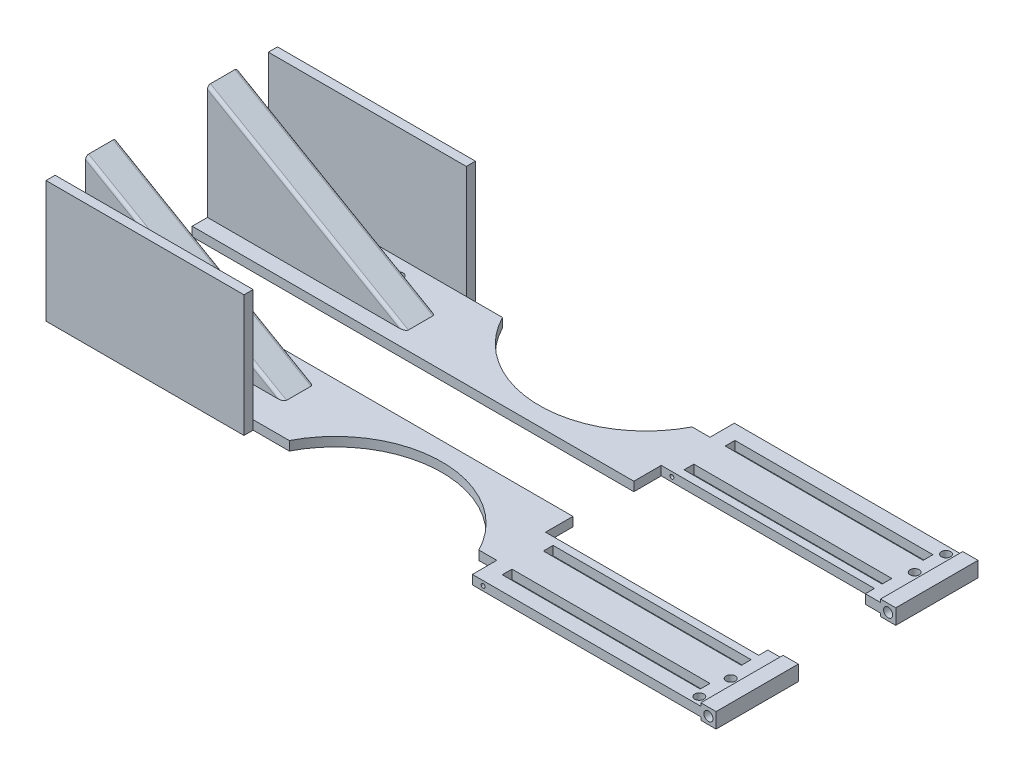
SolidWorks part; units mm, degrees
ref_plane "前视基准面" through (0, 0, 0) normal (0, 0, 1) x (1, 0, 0)
ref_plane "上视基准面" through (0, 0, 0) normal (0, 1, 0) x (1, 0, 0)
ref_plane "右视基准面" through (0, 0, 0) normal (1, 0, 0) x (0, 0, -1)
sketch "草图1" plane through (0, 0, 0) normal (0, 1, 0) x (1, 0, 0)
  line L0 (-92.9537, 0) -> (133.3808, 0) construction
  line L1 (0, 79.573) -> (0, -79.8577) construction
  line L2 (-82.7046, -35) -> (-82.7046, 35)
  line L3 (-82.7046, 35) -> (137.2954, 35)
  line L4 (137.2954, 35) -> (137.2954, -35)
  line L5 (-82.7046, -35) -> (137.2954, -35)
  point P10 (137.2954, 0)
  point P11 (-82.7046, 0)
  dimension "D1" = 70
  dimension "D2" = 220
extrude "凸台-拉伸1" add sketch "草图1" along normal blind 3
sketch "草图2" plane through (0, 0, 0) normal (0, 0, 1) x (1, 0, 0)
  line L0 (-2.7046, 3) -> (-2.7046, 43.2178) construction
  line L2 (59.2954, 3) -> (59.2954, 47.8617) construction
  line L3 (-82.7046, 3) -> (-82.7046, 0) construction
  line L5 (-82.7046, 40.5278) -> (-82.7046, 3)
  line L10 (-82.7046, 3) -> (-17.7046, 3)
  line L11 (-82.7046, 40.5278) -> (-17.7046, 3)
  dimension "D1" = 62
  dimension "D2" = 80
  dimension "D3" = 30
  dimension "D4" = 65
extrude "凸台-拉伸2" add sketch "草图2" along normal blind 25 and the other way blind 25
sketch "草图6" plane through (-82.7046, 0, 0) normal (-1, 0, 0) x (0, 0, 1)
  line L0 (0, 40.5278) -> (0, 0) construction
  line L1 (-25, 40.5278) -> (25, 40.5278) construction
  line L2 (-15, 40.5278) -> (-15, 3)
  line L3 (-15, 3) -> (15, 3)
  line L4 (15, 3) -> (15, 40.5278)
  line L5 (15, 40.5278) -> (-15, 40.5278)
  dimension "D1" = 15
  dimension "D2" = 15
extrude "切除-拉伸4" cut sketch "草图6" against normal through all
sketch "草图7" plane through (0, 3, 0) normal (0, 1, 0) x (1, 0, 0)
  line L0 (-2.7046, 35) -> (-2.7046, -35) construction
  line L4 (137.2954, 35) -> (-82.7046, 35) construction
  line L5 (-82.7046, -35) -> (137.2954, -35) construction
  line L6 (-82.7046, 35) -> (-82.7046, 25) construction
  line L7 (53.2954, 35) -> (53.2954, -35) construction
  line L8 (25.2954, 88.1076) -> (25.2954, -100.7895) construction
  line L9 (-82.7046, 0) -> (117.2954, 0) construction
  line L11 (-82.7046, 15) -> (-82.7046, -15) construction
  circle A0 centre (25.2954, 51) radius 35
  circle A1 centre (25.2954, -51) radius 35
  dimension "D4" = 70
  dimension "D1" = 80
  dimension "D2" = 56
  dimension "D3" = 28
  dimension "D5" = 102
extrude "切除-拉伸5" cut sketch "草图7" against normal through all
sketch "草图8" plane through (-82.7046, 0, 0) normal (-1, 0, 0) x (0, 0, 1)
  line L0 (35, 0) -> (35, 40)
  line L1 (35, 40) -> (38, 40)
  line L2 (38, 40) -> (38, 0)
  line L3 (38, 0) -> (35, 0)
  line L4 (0, 36.5043) -> (0, -13.2047) construction
  line L5 (-38, 0) -> (-35, 0)
  line L6 (-38, 40) -> (-38, 0)
  line L7 (-35, 40) -> (-38, 40)
  line L8 (-35, 0) -> (-35, 40)
  dimension "D1" = 3
  dimension "D2" = 40
extrude "凸台-拉伸3" add sketch "草图8" against normal blind 65
sketch "草图9" plane through (0, 3, 0) normal (0, 1, 0) x (1, 0, 0)
  line L0 (-82.7046, 15) -> (-82.7046, -15) construction
  line L1 (-82.7046, 0) -> (117.2954, 0) construction
  circle A0 centre (-74.7668, 29.8601) radius 1.5
  circle A1 centre (-54.7668, 29.8601) radius 1.5
  circle A2 centre (-34.7668, 29.8601) radius 1.5
  circle A3 centre (-34.7668, -29.8601) radius 1.5
  circle A4 centre (-54.7668, -29.8601) radius 1.5
  circle A5 centre (-74.7668, -29.8601) radius 1.5
  dimension "D1" = 3
  dimension "D2" = 3
extrude "切除-拉伸6" cut sketch "草图9" against normal through all
fillet "圆角5" radius 1 4 edges at (-50.2046, 21.7639, -15) (-50.2046, 21.7639, 15) (-50.2046, 21.7639, 25) (-50.2046, 21.7639, -25)
sketch "草图10" plane through (0, 3, 0) normal (0, 1, 0) x (1, 0, 0)
  line L0 (-82.7046, 0) -> (137.2954, 0) construction
  line L1 (-82.7046, 15) -> (-82.7046, -15) construction
  line L2 (137.2954, 35) -> (137.2954, -35) construction
  line L3 (-82.7046, -10) -> (-82.7046, 10)
  line L4 (-82.7046, 10) -> (-17.7046, 10)
  line L5 (-17.7046, 10) -> (-17.7046, -10)
  line L6 (-82.7046, -10) -> (-17.7046, -10)
  point P11 (-17.7046, 0)
  dimension "D1" = 20
extrude "切除-拉伸7" cut sketch "草图10" against normal through all
sketch "草图11" plane through (0, 3, 0) normal (0, 1, 0) x (1, 0, 0)
  line L0 (137.2954, 0) -> (-17.7046, 0) construction
  line L1 (137.2954, -35) -> (137.2954, 35) construction
  line L2 (-17.7046, -10) -> (-17.7046, 10) construction
  line L3 (62.2954, 43) -> (137.2954, 35) construction
  line L4 (137.2954, 35) -> (62.2954, 35)
  line L5 (137.2954, 35) -> (137.2954, 43)
  line L6 (137.2954, 43) -> (62.2954, 43)
  line L7 (62.2954, 35) -> (62.2954, 43)
  line L8 (62.2954, 35) -> (137.2954, 43) construction
  line L9 (137.2954, -35) -> (137.2954, -43)
  line L10 (67.2954, 38.2) -> (132.2954, 38.2)
  line L11 (67.2954, 38.2) -> (67.2954, 35)
  line L12 (67.2954, 35) -> (132.2954, 35)
  line L13 (132.2954, 38.2) -> (132.2954, 35)
  line L14 (67.2954, 38.2) -> (132.2954, 35) construction
  line L15 (67.2954, 35) -> (132.2954, 38.2) construction
  line L16 (137.2954, -43) -> (62.2954, -43)
  line L17 (62.2954, -35) -> (62.2954, -43)
  line L18 (137.2954, -35) -> (62.2954, -35)
  line L19 (67.2954, -35) -> (132.2954, -35)
  line L20 (132.2954, -38.2) -> (132.2954, -35)
  line L21 (67.2954, -38.2) -> (132.2954, -38.2)
  line L22 (67.2954, -38.2) -> (67.2954, -35)
  point P12 (102.2954, 39)
  line M27 (56.4241, -35) -> (137.2954, -35)
  line M29 (137.2954, 35) -> (56.4241, 35)
  dimension "D1" = 75
  dimension "D2" = 3.2
  dimension "D3" = 8
  dimension "D4" = 65
  dimension "D5" = 5
extrude "网球卡槽" add sketch "草图11" against normal blind 3 contours L10 L13 L5 L6 L7 L4 L11 M29 | L21 L22 L17 L16 L9 L20 M27
sketch "草图12" plane through (0, 3, 0) normal (0, 1, 0) x (1, 0, 0)
  line L0 (-17.7046, 0) -> (137.2954, 0) construction
  line L1 (-17.7046, -10) -> (-17.7046, 10) construction
  line L2 (137.2954, -43) -> (137.2954, 43) construction
  line L3 (67.2954, -21.5) -> (67.2954, -24.7)
  line L4 (132.2954, 21.5) -> (67.2954, 21.5)
  line L5 (132.2954, 21.5) -> (132.2954, 24.7)
  line L6 (132.2954, 24.7) -> (67.2954, 24.7)
  line L7 (67.2954, 21.5) -> (67.2954, 24.7)
  line L8 (132.2954, -24.7) -> (67.2954, -24.7)
  line L9 (132.2954, -21.5) -> (132.2954, -24.7)
  line L10 (132.2954, -21.5) -> (67.2954, -21.5)
  dimension "D1" = 3.2
  dimension "D2" = 65
  dimension "D3" = 43
extrude "乒乓卡槽" cut sketch "草图12" against normal blind 3
sketch "草图13" plane through (0, 3, 0) normal (0, 1, 0) x (1, 0, 0)
  line L0 (-17.7046, 0) -> (137.2954, 0) construction
  line L1 (-17.7046, -10) -> (-17.7046, 10) construction
  line L2 (137.2954, -43) -> (137.2954, 43) construction
  line L3 (62.2954, -19) -> (62.2954, 19)
  line L4 (132.2954, 21.5) -> (132.2954, 24.7) construction
  line L5 (132.2954, -16) -> (137.2954, -16)
  line L6 (62.2954, 19) -> (132.2954, 19)
  line L7 (132.2954, 19) -> (132.2954, 16)
  line L8 (132.2954, 16) -> (137.2954, 16)
  line L9 (137.2954, 16) -> (137.2954, 0)
  line L10 (62.2954, 35) -> (62.2954, 43) construction
  line L12 (132.2954, -19) -> (132.2954, -16)
  line L13 (62.2954, -19) -> (132.2954, -19)
  point P24 (62.2954, 0)
  dimension "D1" = 38
  dimension "D2" = 3
extrude "切除-拉伸9" cut sketch "草图13" against normal blind 3 and the other way through all
sketch "草图14" plane through (0, 0, 43) normal (0, 0, 1) x (1, 0, 0)
  line L0 (62.2954, 1.5) -> (137.2954, 1.5) construction
  line L1 (62.2954, 0) -> (62.2954, 3) construction
  line L2 (137.2954, 0) -> (137.2954, 3) construction
  circle A0 centre (65.7954, 1.5) radius 0.65
  dimension "D1" = 1.3
  dimension "D2" = 3.5
extrude "切除-拉伸10" cut sketch "草图14" against normal through all
sketch "草图17" plane through (137.2954, 0, 0) normal (1, 0, 0) x (0, 0, -1)
  line L0 (16, 1.5) -> (43, 1.5) construction
  line L1 (16, 3) -> (16, 0) construction
  line L2 (43, 0) -> (43, 3) construction
  line L4 (16, -1) -> (16, 4)
  line L5 (16, 40.5278) -> (16, 3) construction
  line L6 (16, 4) -> (43, 4)
  line L7 (43, 4) -> (43, -1)
  line L8 (16, -1) -> (43, -1)
  line L9 (0, 14.7097) -> (0, -14.5497) construction
  line L10 (-16, 4) -> (-43, 4)
  line L11 (-16, -1) -> (-16, 4)
  line L12 (-16, -1) -> (-43, -1)
  line L13 (-43, 4) -> (-43, -1)
  dimension "D1" = 5
extrude "凸台-拉伸4" add sketch "草图17" along normal blind 5
sketch "草图19" plane through (0, 0, -43) normal (0, 0, -1) x (-1, 0, 0)
  line L0 (-142.2954, -1) -> (-142.2954, 4) construction
  circle A0 centre (-139.7954, 1.4356) radius 1.5
  dimension "D1" = 3
  dimension "D2" = 2.5
extrude "切除-拉伸11" cut sketch "草图19" against normal through all
sketch "草图20" plane through (0, 3, 0) normal (0, 1, 0) x (1, 0, 0)
  line L0 (137.2954, 43) -> (137.2954, 16) construction
  line L1 (62.2954, 0) -> (157.0701, 0) construction
  line L2 (62.2954, 19) -> (62.2954, -19) construction
  line L3 (137.2954, 43) -> (62.2954, 43) construction
  circle A0 centre (134.2954, 30.2029) radius 1.5
  circle A1 centre (134.2954, -30.2029) radius 1.5
  circle A2 centre (134.2954, 40.5) radius 1.5
  circle A3 centre (134.2954, -40.5) radius 1.5
  dimension "D1" = 3
  dimension "D3" = 3
  dimension "D4" = 2.5
  dimension "D2" = 3
extrude "切除-拉伸12" cut sketch "草图20" against normal through all
sketch "草图21" plane through (0, 3, 0) normal (0, 1, 0) x (1, 0, 0)
  line L0 (-17.7046, 10) -> (62.2954, 10)
  line L1 (62.2954, 19) -> (62.2954, -19) construction
  line L2 (-17.7046, 10) -> (-17.7046, -10)
  line L3 (-17.7046, -10) -> (62.2954, -10)
  line L4 (62.2954, -10) -> (62.2954, 10)
extrude "切除-拉伸15" cut sketch "草图21" against normal blind 10
